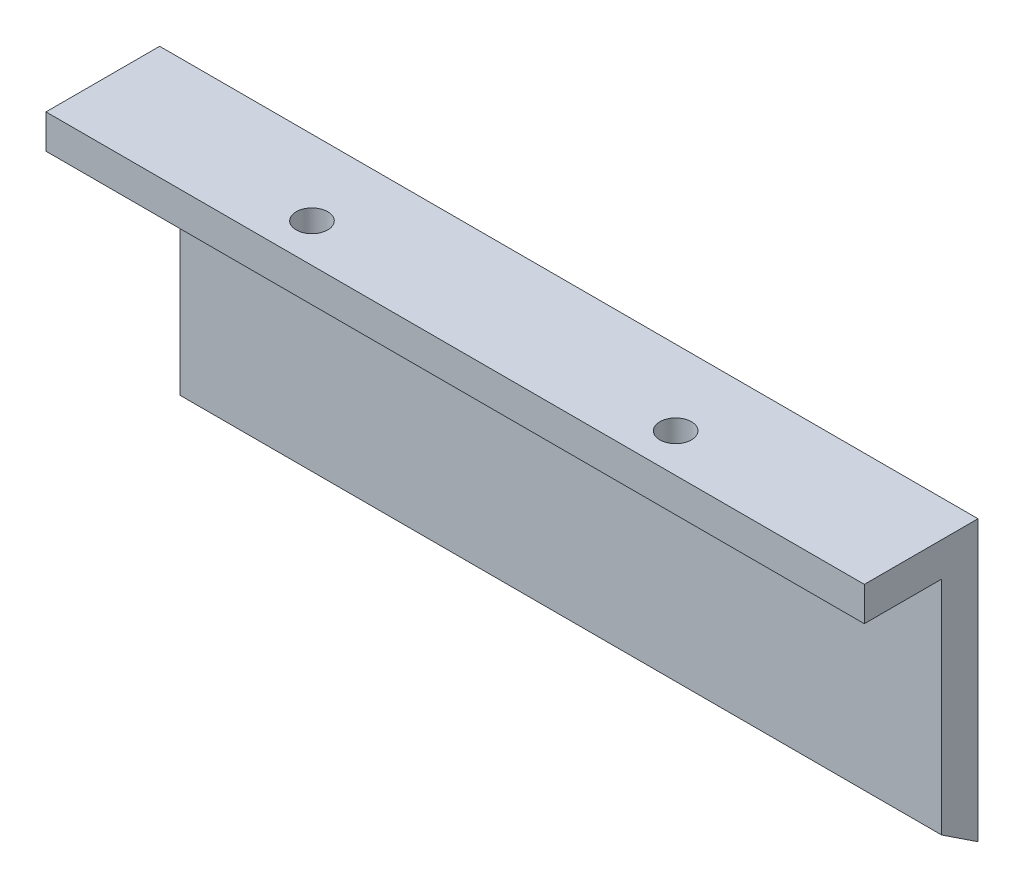
SolidWorks part; units mm, degrees
ref_plane "Front Plane" through (0, 0, 0) normal (0, 0, 1) x (1, 0, 0)
ref_plane "Top Plane" through (0, 0, 0) normal (0, 1, 0) x (1, 0, 0)
ref_plane "Right Plane" through (0, 0, 0) normal (1, 0, 0) x (0, 0, -1)
sketch "Sketch1" plane through (0, 0, 0) normal (1, 0, 0) x (0, 0, -1)
  line L0 (0, 0) -> (-3.2, 2.1124)
  line L1 (-3.2, 2.1124) -> (-3.2, 21.6124)
  line L2 (-3.2, 21.6124) -> (0, 21.6124)
  line L3 (0, 21.6124) -> (0, 0)
  dimension "D1" = 56.57
  dimension "D2" = 3.2
  dimension "D3" = 19.5
extrude "Boss-Extrude1" add sketch "Sketch1" along normal blind 67
sketch "Sketch2" plane through (0, 21.6124, 0) normal (0, 1, 0) x (1, 0, 0)
  line L1 (67, 0) -> (-5, 0)
  line L2 (67, 0) -> (67, -10)
  line L3 (67, -10) -> (-5, -10)
  line L4 (-5, 0) -> (-5, -10)
  dimension "D1" = 10
  dimension "D2" = 72
extrude "Boss-Extrude2" add sketch "Sketch2" along normal blind 3
sketch "Sketch3" plane through (0, 21.6124, 0) normal (0, -1, 0) x (1, 0, 0)
  line L0 (67, 6.6) -> (-5, 6.6) construction
  line L1 (67, 10) -> (67, 3.2) construction
  line L2 (-5, 0) -> (-5, 10) construction
  circle A0 centre (47, 6.6) radius 1.3891
  circle A1 centre (15, 6.6) radius 1.3891
  dimension "D1" = 2.7781
  dimension "D2" = 2.7781
  dimension "D3" = 20
  dimension "D4" = 20
extrude "Cut-Extrude1" cut sketch "Sketch3" against normal up to surface (3 mm away) up to face at (31, 24.6124, 5)
